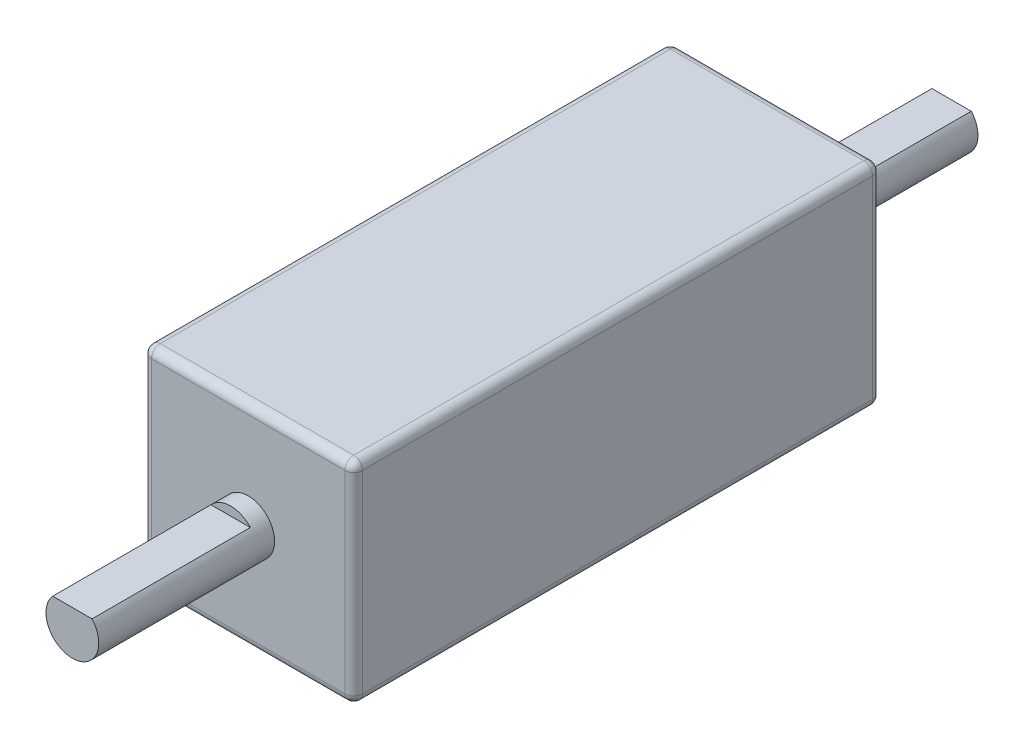
SolidWorks part; units mm, degrees
ref_plane "前视基准面" through (0, 0, 0) normal (0, 0, 1) x (1, 0, 0)
ref_plane "上视基准面" through (0, 0, 0) normal (0, 1, 0) x (1, 0, 0)
ref_plane "右视基准面" through (0, 0, 0) normal (1, 0, 0) x (0, 0, -1)
sketch "草图1" plane through (0, 0, 0) normal (0, 0, 1) x (1, 0, 0)
  line L1 (-6, -6) -> (6, -6)
  line L2 (-6, -6) -> (-6, 6)
  line L3 (-6, 6) -> (6, 6)
  line L4 (6, -6) -> (6, 6)
  line L5 (-6, -6) -> (6, 6) construction
  line L6 (-6, 6) -> (6, -6) construction
  point P0 (0, 0)
  dimension "D1" = 12
  dimension "D2" = 12
extrude "凸台-拉伸1" add sketch "草图1" along normal blind 30
sketch "草图2" plane through (0, 0, 30) normal (0, 0, 1) x (1, 0, 0)
  circle A0 centre (0, 0) radius 1.5
extrude "凸台-拉伸2" add sketch "草图2" along normal blind 10
fillet "圆角1" radius 0.5 12 edges at (0, -6, 0) (-6, 0, 0) (0, 6, 0) (6, 0, 0) (6, 0, 30) (0, 6, 30) (-6, 0, 30) (0, -6, 30) (-6, -6, 15) (-6, 6, 15) (6, 6, 15) (6, -6, 15)
sketch "草图3" plane through (0, 0, 40) normal (0, 0, 1) x (1, 0, 0)
  line L1 (-1.118, 1) -> (1.118, 1)
  circle A0 centre (0, 0) radius 1.5 construction
extrude "切除-拉伸1" cut sketch "草图3" against normal blind 9 and the other way through all
sketch "草图4" plane through (0, 0, 0) normal (0, 0, -1) x (-1, 0, 0)
  circle A0 centre (0, 0) radius 1.5
extrude "凸台-拉伸3" add sketch "草图4" along normal blind 10
sketch "草图5" plane through (0, 0, -10) normal (0, 0, -1) x (-1, 0, 0)
  line L1 (1.118, 1) -> (-1.118, 1)
  circle A0 centre (0, 0) radius 1.5 construction
  circle A1 centre (0, 0) radius 1.5 construction
extrude "切除-拉伸3" cut sketch "草图5" against normal blind 9 and the other way through all flip side to cut
